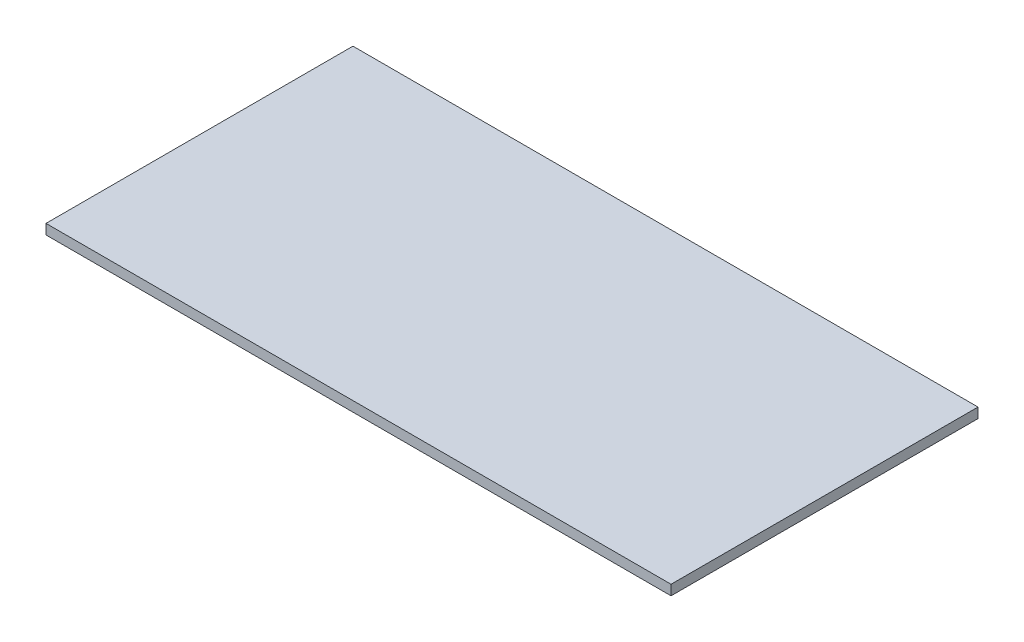
SolidWorks part; units mm, degrees
ref_plane "Спереди" through (0, 0, 0) normal (0, 0, 1) x (1, 0, 0)
ref_plane "Сверху" through (0, 0, 0) normal (0, 1, 0) x (1, 0, 0)
ref_plane "Справа" through (0, 0, 0) normal (1, 0, 0) x (0, 0, -1)
sketch "Эскиз1" plane through (0, 0, 0) normal (0, 1, 0) x (1, 0, 0)
  line L1 (560, -275) -> (-560, -275)
  line L2 (560, -275) -> (560, 275)
  line L3 (560, 275) -> (-560, 275)
  line L4 (-560, -275) -> (-560, 275)
  line L5 (560, -275) -> (-560, 275) construction
  line L6 (560, 275) -> (-560, -275) construction
  point P0 (0, 0)
  dimension "D1" = 1120
  dimension "D2" = 550
extrude "Бобышка-Вытянуть1" add sketch "Эскиз1" along normal blind 18
